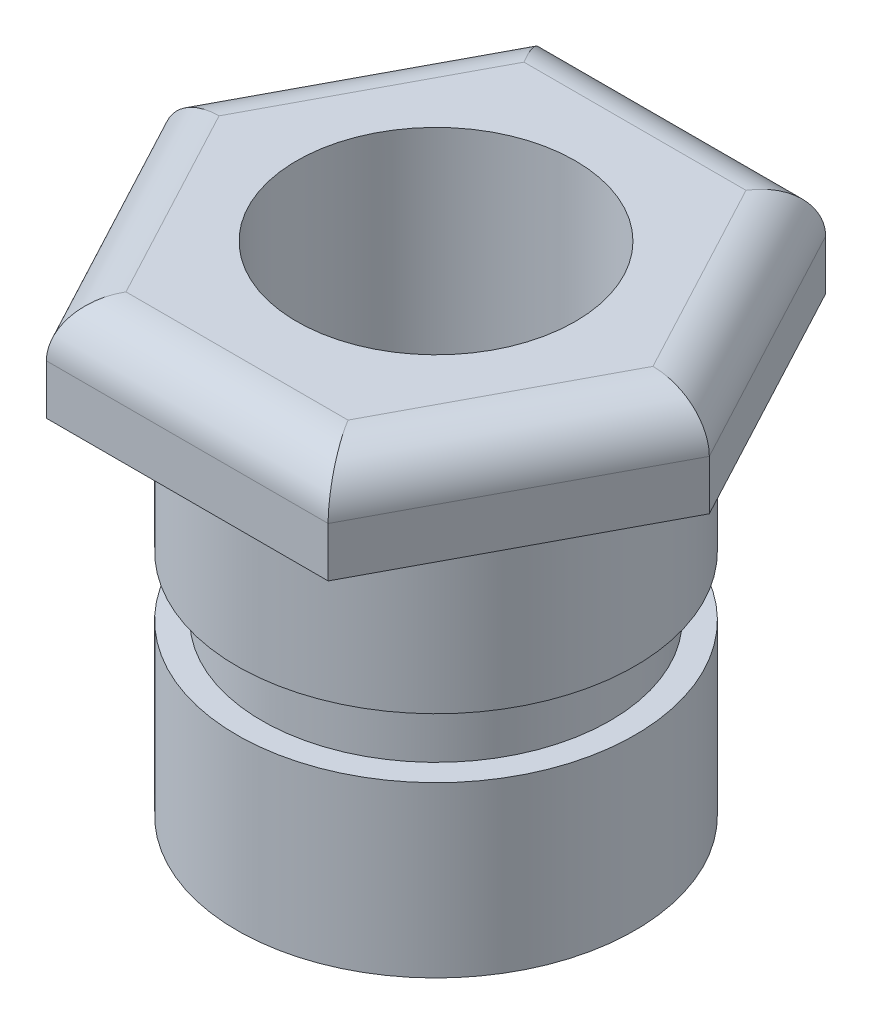
SolidWorks part; units mm, degrees
ref_plane "Front Plane" through (0, 0, 0) normal (0, 0, 1) x (1, 0, 0)
ref_plane "Top Plane" through (0, 0, 0) normal (0, 1, 0) x (1, 0, 0)
ref_plane "Right Plane" through (0, 0, 0) normal (1, 0, 0) x (0, 0, -1)
sketch "Sketch1" plane through (0, 0, 0) normal (0, 0, 1) x (1, 0, 0)
  line L0 (0, 103.4121) -> (0, -60.6995) construction
  line L1 (0, 0) -> (40, 0)
  line L2 (40, 0) -> (40, 34)
  line L3 (40, 34) -> (35, 34)
  line L4 (35, 34) -> (35, 46)
  line L5 (35, 46) -> (40, 46)
  line L6 (40, 46) -> (40, 80)
  line L7 (40, 80) -> (0, 80)
  line L8 (0, 0) -> (0, 80)
  point P5 (0, 58.6092)
  point P12 (-4.5041, 80)
  point P13 (0, 0)
  point P14 (40, 46)
  point P15 (0, 103.4121)
  dimension "D1" = 80
  dimension "D2" = 34
  dimension "D3" = 12
  dimension "D4" = 70
  dimension "D5" = 34
revolve "Revolve1" add sketch "Sketch1" angle 360 about L0
sketch "Sketch2" plane through (0, 80, 0) normal (0, 1, 0) x (1, 0, 0)
  line L0 (0, 71.7601) -> (0, -72.5011) construction
  line L1 (-28.3217, 50) -> (28.3217, 50)
  line L2 (28.3217, 50) -> (54.9387, 0)
  line L3 (54.9387, 0) -> (28.3217, -50)
  line L4 (28.3217, -50) -> (-28.3217, -50)
  line L5 (-28.3217, -50) -> (-54.9387, 0)
  line L6 (-54.9387, 0) -> (-28.3217, 50)
  point P8 (0, 0)
  point P10 (0, 0)
  point P11 (0, 0)
  dimension "D1" = 100
extrude "Boss-Extrude1" add sketch "Sketch2" along normal blind 20
fillet "Fillet1" radius 10 6 edges at (0, 100, 50) (41.6302, 100, 25) (41.6302, 100, -25) (0, 100, -50) (-41.6302, 100, -25) (-41.6302, 100, 25)
sketch "Sketch5" plane through (0, 0, 0) normal (0, -1, 0) x (1, 0, 0)
  circle A0 centre (0, 0) radius 28
  dimension "D1" = 56
extrude "Cut-Extrude1" cut sketch "Sketch5" against normal up to next
